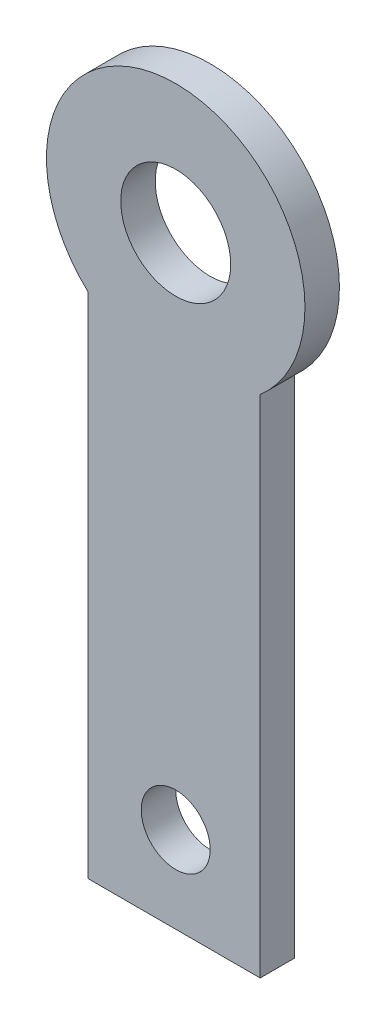
SolidWorks part; units mm, degrees
material "6061-T4 (SS)"
ref_plane "Front Plane" through (0, 0, 0) normal (0, 0, 1) x (1, 0, 0)
ref_plane "Top Plane" through (0, 0, 0) normal (0, 1, 0) x (1, 0, 0)
ref_plane "Right Plane" through (0, 0, 0) normal (1, 0, 0) x (0, 0, -1)
sketch "Sketch1" plane through (0, 0, 0) normal (0, 0, 1) x (1, 0, 0)
  line L0 (15.5, 0) -> (15.5, 8) construction
  line L1 (11, 0) -> (20, 0) construction
  line L2 (12.9503, 5.2502) -> (12.9503, -9.5)
  line L3 (12.9503, -9.5) -> (17.9503, -9.5)
  line L4 (17.9503, -9.5) -> (17.9503, 5.1612)
  line L5 (15.5, 5.2048) -> (15.5, -7) construction
  arc A0 (12.9503, 5.2502) -> (17.9503, 5.1612) centre (15.5, 8) cw
  circle A1 centre (15.5, 8) radius 1.595
  circle A2 centre (15.5, -7) radius 1
  dimension "D2" = 3.75
  dimension "D5" = 3.19
  dimension "D7" = 2
  dimension "D1" = 8
  dimension "D3" = 15
  dimension "D4" = 5
  dimension "D6" = 17.5
  dimension "D8" = 4.5
extrude "Boss-Extrude1" add sketch "Sketch1" along normal blind 1
